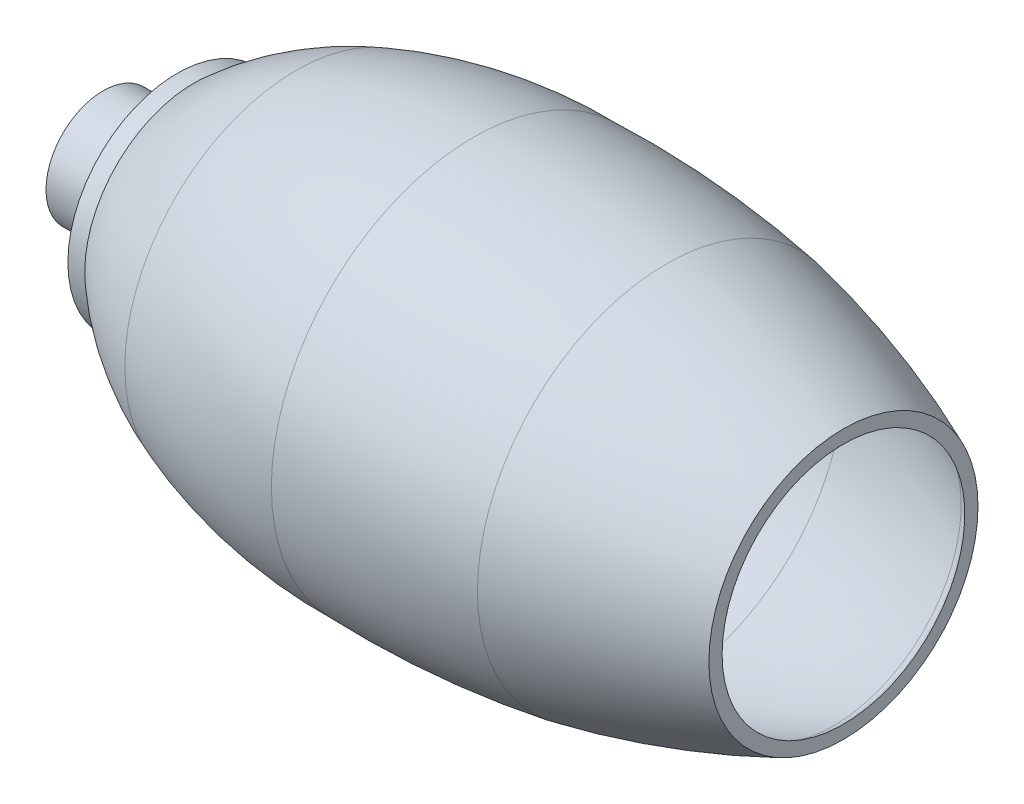
SolidWorks part; units mm, degrees
ref_plane "Front Plane" through (0, 0, 0) normal (0, 0, 1) x (1, 0, 0)
ref_plane "Top Plane" through (0, 0, 0) normal (0, 1, 0) x (1, 0, 0)
ref_plane "Right Plane" through (0, 0, 0) normal (1, 0, 0) x (0, 0, -1)
sketch "Sketch2" plane through (0, 0, 0) normal (0, 0, 1) x (1, 0, 0)
  line L0 (536.8333, 878.5) -> (2684.1667, 878.5) construction
  line L5 (0, 73.993) -> (13.6383, 73.993)
  line L6 (0, 60.0046) -> (219.9886, 60.0046) construction
  line L7 (13.6383, 73.993) -> (23.6339, 89.4917)
  line L8 (23.6339, 89.4917) -> (28.1653, 89.4917)
  line L9 (0, 76.993) -> (0, 73.993)
  line L11 (219.9886, 96.0677) -> (219.9886, 99.9937)
  line L23 (0, 76.993) -> (12.0033, 76.993)
  line L28 (12.0033, 76.993) -> (21.9989, 92.4917)
  line L29 (21.9989, 92.4917) -> (27.0022, 92.4917)
  line L33 (216.9886, 60.0046) -> (216.9886, 98.0024) construction
  line L34 (219.9886, 60.0046) -> (219.9886, 99.9937) construction
  arc A0 (27.0022, 92.4917) -> (57.3095, 110.8837) centre (90.4804, 22.056) cw
  arc A1 (57.3095, 110.8837) -> (109.9943, 120.0091) centre (107.9141, -24.6295) cw
  arc A2 (109.9943, 120.0091) -> (167.402, 116.1731) centre (119.1689, -174.1734) cw
  arc A3 (167.402, 116.1731) -> (219.9886, 99.9937) centre (116.2838, -143.5205) cw
  arc A4 (28.1653, 89.4917) -> (58.359, 108.0733) centre (90.4804, 22.056) cw
  arc A5 (58.359, 108.0733) -> (110.0193, 117.0084) centre (107.9141, -24.6295) cw
  arc A6 (110.0193, 117.0084) -> (166.8664, 113.221) centre (119.1689, -174.1734) cw
  arc A7 (166.8664, 113.221) -> (216.9886, 98.0024) centre (116.2838, -143.5205) cw
  arc A8 (216.9886, 98.0024) -> (219.9886, 96.0677) centre (213.5757, 89.4174) cw
  dimension "D1" = 3
revolve "Revolve2" add sketch "Sketch2" angle 360 about L6
